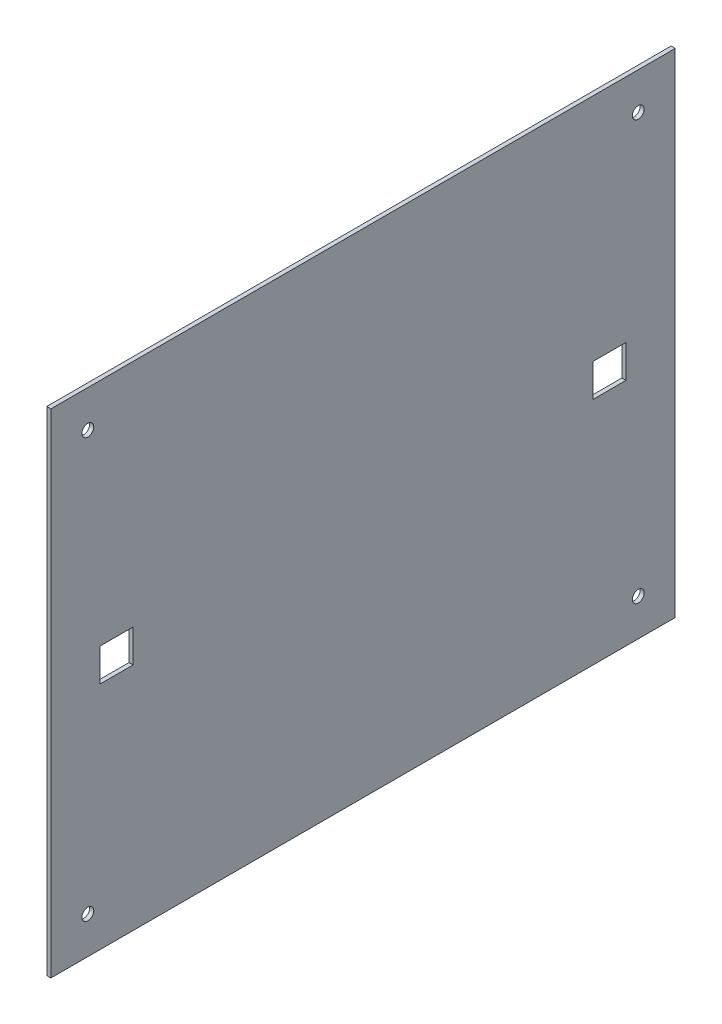
SolidWorks part; units mm, degrees
ref_plane "Front Plane" through (0, 0, 0) normal (0, 0, 1) x (1, 0, 0)
ref_plane "Top Plane" through (0, 0, 0) normal (0, 1, 0) x (1, 0, 0)
ref_plane "Right Plane" through (0, 0, 0) normal (1, 0, 0) x (0, 0, -1)
sketch "Sketch1" plane through (0, 0, 0) normal (1, 0, 0) x (0, 0, -1)
  line L1 (0, 0) -> (241.3, 0)
  line L2 (0, 0) -> (0, 190.5)
  line L3 (0, 190.5) -> (241.3, 190.5)
  line L4 (241.3, 0) -> (241.3, 190.5)
  dimension "D1" = 241.3
  dimension "D2" = 190.5
extrude "Boss-Extrude1" add sketch "Sketch1" along normal blind 1.5875
sketch "Sketch2" plane through (1.5875, 0, 0) normal (1, 0, 0) x (0, 0, -1)
  line L2 (-1000, 95.25) -> (49000, 95.25) construction
  line L3 (0, 190.5) -> (0, 0) construction
  line L4 (120.65, -809.5) -> (120.65, 49190.5) construction
  line L5 (241.3, 190.5) -> (0, 190.5) construction
  line L6 (1228.6, 95.25) -> (-48771.4, 95.25) construction
  line L7 (241.3, 0) -> (241.3, 190.5) construction
  line L8 (0, 0) -> (241.3, 0) construction
  circle A8 centre (227.0125, 14.2875) radius 2.286
  circle A9 centre (227.0125, 176.2125) radius 2.286
  circle A10 centre (14.2875, 14.2875) radius 2.286
  circle A11 centre (14.2875, 176.2125) radius 2.286
  point P15 (0, 95.25)
  point P20 (120.65, 190.5)
  dimension "D1" = 4.572
  dimension "D2" = 14.2875
  dimension "D3" = 14.2875
extrude "Cut-Extrude1" cut sketch "Sketch2" against normal through all
sketch "Sketch3" plane through (1.5875, 0, 0) normal (1, 0, 0) x (0, 0, -1)
  line L0 (0, 190.5) -> (0, 0) construction
  line L1 (19.05, 101.6) -> (31.75, 101.6)
  line L2 (19.05, 101.6) -> (19.05, 88.9)
  line L3 (19.05, 88.9) -> (31.75, 88.9)
  line L4 (31.75, 101.6) -> (31.75, 88.9)
  line L5 (209.55, 101.6) -> (222.25, 101.6)
  line L6 (209.55, 101.6) -> (209.55, 88.9)
  line L7 (209.55, 88.9) -> (222.25, 88.9)
  line L8 (222.25, 101.6) -> (222.25, 88.9)
  line L9 (241.3, 0) -> (241.3, 190.5) construction
  point P8 (19.05, 95.25)
  point P9 (209.55, 95.25)
  point P12 (0, 95.25)
  dimension "D1" = 12.7
  dimension "D2" = 12.7
  dimension "D3" = 19.05
  dimension "D4" = 19.05
extrude "Cut-Extrude2" cut sketch "Sketch3" against normal through all
